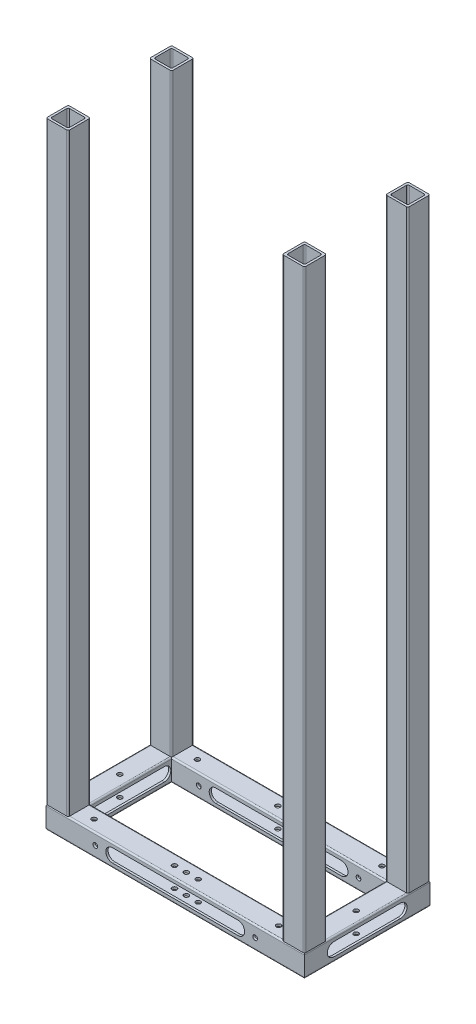
SolidWorks part; units mm, degrees
material "6061 合金"
ref_plane "前视基准面" through (0, 0, 0) normal (0, 0, 1) x (1, 0, 0)
ref_plane "上视基准面" through (0, 0, 0) normal (0, 1, 0) x (1, 0, 0)
ref_plane "右视基准面" through (0, 0, 0) normal (1, 0, 0) x (0, 0, -1)
sketch "草图1" plane through (0, 0, 0) normal (0, 1, 0) x (1, 0, 0)
  line L1 (-80, 35) -> (80, 35)
  line L2 (-80, 35) -> (-80, -35)
  line L3 (-80, -35) -> (80, -35)
  line L4 (80, 35) -> (80, -35)
  line L5 (-80, 35) -> (80, -35) construction
  line L6 (-80, -35) -> (80, 35) construction
  point P0 (0, 0)
  dimension "D1" = 160
  dimension "D2" = 70
sketch3d "3D草图1"
  line L0 (-80, 0, -35) -> (-80, 410, -35)
  line L1 (-80, 0, 35) -> (-80, 410, 35)
  line L2 (80, 0, -35) -> (80, 410, -35)
  line L3 (80, 0, 35) -> (80, 410, 35)
  dimension "D1" = 410
  dimension "D2" = 410
  dimension "D3" = 410
  dimension "D4" = 410
other "结构构件1"
ref_plane "基准面1" through (-80, 0, 35) normal (1, 0, 0) x (0, 0, -1)
sketch "草图11" plane through (-80, 0, 35) normal (1, 0, 0) x (0, 0, -1)
  line L0 (-5, 6) -> (5, 6)
  line L1 (-6.5, 7.5) -> (6.5, 7.5)
  line L2 (-7.5, 6.5) -> (-7.5, -6.5)
  line L3 (-6.5, -7.5) -> (6.5, -7.5)
  line L4 (7.5, 6.5) -> (7.5, -6.5)
  line L5 (-7.5, 7.5) -> (7.5, -7.5) construction
  line L6 (-7.5, -7.5) -> (7.5, 7.5) construction
  line L7 (6, 5) -> (6, -5)
  line L8 (-5, -6) -> (5, -6)
  line L9 (-6, 5) -> (-6, -5)
  line L10 (6, 6) -> (6, -6) construction
  line L11 (-6, 6) -> (6, 6) construction
  line L12 (-6, -6) -> (6, -6) construction
  line L13 (-6, 6) -> (-6, -6) construction
  line L14 (-7.5, 7.5) -> (7.5, 7.5) construction
  line L15 (7.5, 7.5) -> (7.5, -7.5) construction
  line L16 (-7.5, -7.5) -> (7.5, -7.5) construction
  line L17 (-7.5, 7.5) -> (-7.5, -7.5) construction
  arc A0 (6, 5) -> (5, 6) centre (5, 5) ccw
  arc A1 (6, -5) -> (5, -6) centre (5, -5) cw
  arc A2 (-5, -6) -> (-6, -5) centre (-5, -5) cw
  arc A3 (-6, 5) -> (-5, 6) centre (-5, 5) cw
  arc A4 (6.5, 7.5) -> (7.5, 6.5) centre (6.5, 6.5) cw
  arc A5 (7.5, -6.5) -> (6.5, -7.5) centre (6.5, -6.5) cw
  arc A6 (-6.5, -7.5) -> (-7.5, -6.5) centre (-6.5, -6.5) cw
  arc A7 (-7.5, 6.5) -> (-6.5, 7.5) centre (-6.5, 6.5) cw
  point P0 (0, 0)
  point P34 (0, 0)
  dimension "D4" = 1
  dimension "D1" = 15
  dimension "D2" = 15
  dimension "D3" = 1.5
other "结构构件2"
ref_plane "基准面2" through (-80, 0, 35) normal (0, 1, 0) x (1, 0, 0)
sketch "草图12" plane through (-80, 0, 35) normal (0, 1, 0) x (1, 0, 0)
  line L0 (-5, 6) -> (5, 6)
  line L1 (-6.5, 7.5) -> (6.5, 7.5)
  line L2 (-7.5, 6.5) -> (-7.5, -6.5)
  line L3 (-6.5, -7.5) -> (6.5, -7.5)
  line L4 (7.5, 6.5) -> (7.5, -6.5)
  line L5 (-7.5, 7.5) -> (7.5, -7.5) construction
  line L6 (-7.5, -7.5) -> (7.5, 7.5) construction
  line L7 (6, 5) -> (6, -5)
  line L8 (-5, -6) -> (5, -6)
  line L9 (-6, 5) -> (-6, -5)
  line L10 (6, 6) -> (6, -6) construction
  line L11 (-6, 6) -> (6, 6) construction
  line L12 (-6, -6) -> (6, -6) construction
  line L13 (-6, 6) -> (-6, -6) construction
  line L14 (-7.5, 7.5) -> (7.5, 7.5) construction
  line L15 (7.5, 7.5) -> (7.5, -7.5) construction
  line L16 (-7.5, -7.5) -> (7.5, -7.5) construction
  line L17 (-7.5, 7.5) -> (-7.5, -7.5) construction
  arc A0 (6, 5) -> (5, 6) centre (5, 5) ccw
  arc A1 (6, -5) -> (5, -6) centre (5, -5) cw
  arc A2 (-5, -6) -> (-6, -5) centre (-5, -5) cw
  arc A3 (-6, 5) -> (-5, 6) centre (-5, 5) cw
  arc A4 (6.5, 7.5) -> (7.5, 6.5) centre (6.5, 6.5) cw
  arc A5 (7.5, -6.5) -> (6.5, -7.5) centre (6.5, -6.5) cw
  arc A6 (-6.5, -7.5) -> (-7.5, -6.5) centre (-6.5, -6.5) cw
  arc A7 (-7.5, 6.5) -> (-6.5, 7.5) centre (-6.5, 6.5) cw
  point P0 (0, 0)
  point P34 (0, 0)
  dimension "D4" = 1
  dimension "D1" = 15
  dimension "D2" = 15
  dimension "D3" = 1.5
sketch "草图13" plane through (0, 7.5, 0) normal (0, 1, 0) x (1, 0, 0)
  line L0 (0, -28.5) -> (0, -41.5) construction
  line L1 (73.5, -28.5) -> (-73.5, -28.5) construction
  line L2 (86.5, -41.5) -> (-86.5, -41.5) construction
  line L3 (0, 0) -> (19.1715, 0) construction
  circle A0 centre (0, -35) radius 1.6
  circle A1 centre (0, 35) radius 1.6
  dimension "D1" = 3.2
extrude "切除-拉伸1" cut sketch "草图13" against normal up to surface (15 mm away)
other "剪裁/延伸1"
sketch "草图14" plane through (0, -7.5, 0) normal (0, -1, 0) x (1, 0, 0)
  line L0 (0, 35) -> (-95, 35) construction
  line L1 (0, 0) -> (0, 15.6754) construction
  line L2 (0, 0) -> (30.6032, 0) construction
  circle A0 centre (-95, 35) radius 1.6
  circle A1 centre (95, 35) radius 1.6
  circle A2 centre (95, -35) radius 1.6
  circle A3 centre (-95, -35) radius 1.6
  dimension "D2" = 3.2
  dimension "D1" = 95
sketch "草图15" plane through (0, 0, -42.5) normal (0, 0, -1) x (-1, 0, 0)
  line L0 (0, 6.5) -> (0, -6.5) construction
  line L1 (87.5, 6.5) -> (-87.5, 6.5) construction
  line L2 (87.5, -6.5) -> (-87.5, -6.5) construction
  line L3 (0, 0) -> (-54.11, 0) construction
  circle A0 centre (-54.11, 0) radius 1.6
  circle A1 centre (54.11, 0) radius 1.6
  dimension "D2" = 3.2
  dimension "D1" = 54.11
extrude "切除-拉伸2" cut sketch "草图15" against normal up to surface (85 mm away)
sketch "草图16" plane through (0, 7.5, 0) normal (0, 1, 0) x (1, 0, 0)
  line L0 (86.5, 0) -> (73.5, 0) construction
  line L1 (86.5, 41.5) -> (86.5, -41.5) construction
  line L2 (73.5, 28.5) -> (73.5, -28.5) construction
  line L3 (-73.5, 0) -> (-86.5, 0) construction
  line L4 (-73.5, -28.5) -> (-73.5, 28.5) construction
  line L5 (-86.5, -41.5) -> (-86.5, 41.5) construction
  circle A0 centre (80, 0) radius 1.6
  circle A1 centre (-80, 0) radius 1.6
  dimension "D1" = 3.2
  dimension "D2" = 3.2
extrude "切除-拉伸3" cut sketch "草图16" against normal up to surface (15 mm away)
sketch "草图17" plane through (0, 7.5, 0) normal (0, 1, 0) x (1, 0, 0)
  line L0 (0, 35) -> (8, 35) construction
  line L1 (0, 0) -> (0, 20.8775) construction
  line L2 (0, 0) -> (28.8273, 0) construction
  circle A0 centre (8, 35) radius 1.6
  circle A1 centre (-8, 35) radius 1.6
  circle A2 centre (-8, -35) radius 1.6
  circle A3 centre (8, -35) radius 1.6
  dimension "D2" = 3.2
  dimension "D1" = 8
extrude "切除-拉伸4" cut sketch "草图17" against normal up to surface (15 mm away)
sketch "草图18" plane through (0, 7.5, 0) normal (0, 1, 0) x (1, 0, 0)
  line L0 (-72.5, -35) -> (-62.5, -35) construction
  line L1 (-72.5, -28.5) -> (-72.5, -41.5) construction
  line L2 (0, 0) -> (0, 19.805) construction
  line L3 (0, 0) -> (17.2287, 0) construction
  circle A0 centre (-62.5, -35) radius 1.6
  circle A1 centre (62.5, -35) radius 1.6
  circle A2 centre (62.5, 35) radius 1.6
  circle A3 centre (-62.5, 35) radius 1.6
  dimension "D2" = 3.2
  dimension "D1" = 10
extrude "切除-拉伸5" cut sketch "草图18" against normal up to surface (15 mm away)
sketch "草图22" plane through (0, 0, -42.5) normal (0, 0, -1) x (-1, 0, 0)
  line L0 (-42.5, 0) -> (42.5, 0) construction
  line L1 (-42.5, 4.5) -> (42.5, 4.5)
  line L2 (-42.5, -4.5) -> (42.5, -4.5)
  line L3 (86.5, 7.5) -> (-86.5, 7.5) construction
  line L4 (-87.5, -6.5) -> (-87.5, 6.5) construction
  line L5 (87.5, 6.5) -> (87.5, -6.5) construction
  arc A0 (-42.5, 4.5) -> (-42.5, -4.5) centre (-42.5, 0) ccw
  arc A1 (42.5, -4.5) -> (42.5, 4.5) centre (42.5, 0) ccw
  point P3 (0, 0)
  dimension "D1" = 3
  dimension "D2" = 45
  dimension "D3" = 45
extrude "切除-拉伸7" cut sketch "草图22" against normal blind 85
sketch "草图23" plane through (87.5, 0, 0) normal (1, 0, 0) x (0, 0, -1)
  line L0 (-22.5, 0) -> (22.5, 0) construction
  line L1 (-22.5, 4.5) -> (22.5, 4.5)
  line L2 (-22.5, -4.5) -> (22.5, -4.5)
  line L3 (41.5, 7.5) -> (-41.5, 7.5) construction
  line L4 (-42.5, 6.5) -> (-42.5, -6.5) construction
  line L5 (42.5, -6.5) -> (42.5, 6.5) construction
  arc A0 (-22.5, 4.5) -> (-22.5, -4.5) centre (-22.5, 0) ccw
  arc A1 (22.5, -4.5) -> (22.5, 4.5) centre (22.5, 0) ccw
  point P3 (0, 0)
  dimension "D1" = 3
  dimension "D2" = 20
  dimension "D3" = 20
extrude "切除-拉伸8" cut sketch "草图23" against normal blind 176
